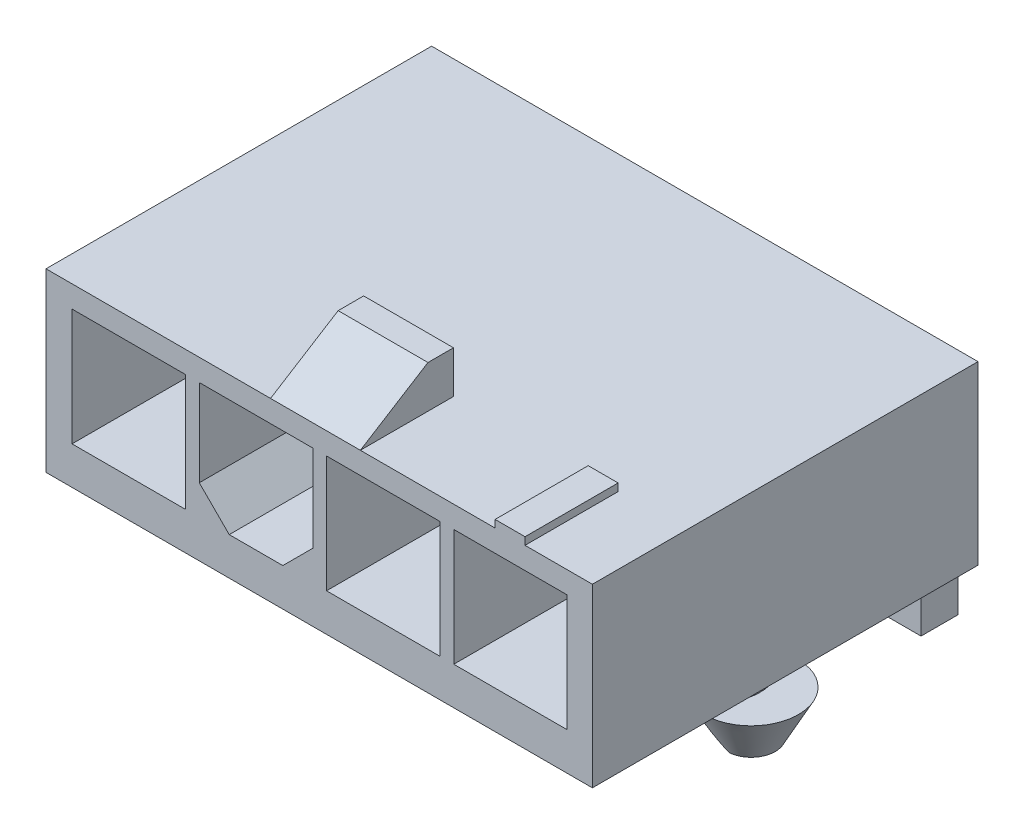
SolidWorks part; units mm, degrees
ref_plane "Front Plane" through (0, 0, 0) normal (0, 0, 1) x (1, 0, 0)
ref_plane "Top Plane" through (0, 0, 0) normal (0, 1, 0) x (1, 0, 0)
ref_plane "Right Plane" through (0, 0, 0) normal (1, 0, 0) x (0, 0, -1)
sketch "Sketch1" plane through (0, 0, 0) normal (0, 1, 0) x (1, 0, 0)
  line L1 (0, 0) -> (18.25, 0)
  line L2 (0, 0) -> (0, 12.88)
  line L3 (0, 12.88) -> (18.25, 12.88)
  line L4 (18.25, 0) -> (18.25, 12.88)
extrude "Boss-Extrude1" add sketch "Sketch1" along normal blind 5.89
sketch "Sketch2" plane through (0, 0, 0) normal (0, 0, 1) x (1, 0, 0)
  line L0 (4.66, 5.1605) -> (5.12, 5.1605) construction
  line L1 (0.87, 5.1605) -> (4.66, 5.1605)
  line L2 (0.87, 5.1605) -> (0.87, 1.2605)
  line L3 (0.87, 1.2605) -> (4.66, 1.2605)
  line L4 (4.66, 5.1605) -> (4.66, 1.2605)
  line L5 (5.12, 5.1605) -> (8.91, 5.1605)
  line L6 (5.12, 5.1605) -> (5.12, 1.2605) construction
  line L7 (5.12, 1.2605) -> (8.91, 1.2605) construction
  line L8 (8.91, 5.1605) -> (8.91, 1.2605) construction
  line L9 (9.37, 5.1605) -> (13.16, 5.1605)
  line L10 (9.37, 5.1605) -> (9.37, 1.2605)
  line L11 (9.37, 1.2605) -> (13.16, 1.2605)
  line L12 (13.16, 5.1605) -> (13.16, 1.2605)
  line L13 (13.62, 5.1605) -> (17.41, 5.1605)
  line L14 (13.62, 5.1605) -> (13.62, 1.2605)
  line L15 (13.62, 1.2605) -> (17.41, 1.2605)
  line L16 (17.41, 5.1605) -> (17.41, 1.2605)
  line L17 (8.91, 5.1605) -> (9.37, 5.1605) construction
  line L18 (13.16, 5.1605) -> (13.62, 5.1605) construction
  line L19 (4.66, 1.2605) -> (5.12, 1.2605) construction
  line L20 (8.91, 1.2605) -> (9.37, 1.2605) construction
  line L21 (5.12, 2.2605) -> (6.12, 1.2605)
  line L22 (13.16, 1.2605) -> (13.62, 1.2605) construction
  line L23 (5.12, 5.1605) -> (5.12, 2.2605)
  line L24 (6.12, 1.2605) -> (7.91, 1.2605)
  line L25 (7.91, 1.2605) -> (8.91, 2.2605)
  line L26 (8.91, 2.2605) -> (8.91, 5.1605)
extrude "Cut-Extrude1" cut sketch "Sketch2" against normal blind 9
sketch "Sketch3" plane through (0, 5.89, 0) normal (0, 1, 0) x (1, 0, 0)
  line L0 (0, 0) -> (18.25, 0) construction
  line L1 (7.5, 0) -> (10.5, 0)
  line L2 (7.5, 0) -> (7.5, 3.11)
  line L3 (7.5, 3.11) -> (10.5, 3.11)
  line L4 (10.5, 0) -> (10.5, 3.11)
extrude "Boss-Extrude2" add sketch "Sketch3" along normal blind 1.41
sketch "Sketch4" plane through (7.5, 0, 0) normal (-1, 0, 0) x (0, 0, 1)
  line L0 (-2.2584, 7.3) -> (0, 5.89)
  line L1 (-3.11, 7.3) -> (0, 7.3) construction
  line L2 (0, 7.3) -> (0, 5.89) construction
  line L3 (0, 5.89) -> (0, 7.3)
  line L4 (0, 7.3) -> (-2.2584, 7.3)
extrude "Cut-Extrude2" cut sketch "Sketch4" against normal blind 3
sketch "Sketch5" plane through (0, 0, -12.88) normal (0, 0, -1) x (-1, 0, 0)
  line L1 (-3.4, 3.26) -> (-2.17, 3.26)
  line L2 (-3.4, 3.26) -> (-3.4, 2.03)
  line L3 (-3.4, 2.03) -> (-2.17, 2.03)
  line L4 (-2.17, 3.26) -> (-2.17, 2.03)
  line L18 (-7.6052, 3.2578) -> (-6.3752, 3.2578)
  line L19 (-7.6052, 3.2578) -> (-7.6052, 2.0278)
  line L20 (-7.6052, 2.0278) -> (-6.3752, 2.0278)
  line L21 (-6.3752, 3.2578) -> (-6.3752, 2.0278)
  line L22 (-11.8105, 3.2556) -> (-10.5805, 3.2556)
  line L23 (-11.8105, 3.2556) -> (-11.8105, 2.0256)
  line L24 (-11.8105, 2.0256) -> (-10.5805, 2.0256)
  line L25 (-10.5805, 3.2556) -> (-10.5805, 2.0256)
  line L26 (-16.0157, 3.2535) -> (-14.7857, 3.2535)
  line L27 (-16.0157, 3.2535) -> (-16.0157, 2.0235)
  line L28 (-16.0157, 2.0235) -> (-14.7857, 2.0235)
  line L29 (-14.7857, 3.2535) -> (-14.7857, 2.0235)
  dimension "D1" = 4
sketch "Sketch7" plane through (0, 0, 0) normal (-1, 0, 0) x (0, 0, 1)
  line L0 (-4.3, 2.72) -> (-12.7005, 2.72)
  line L1 (-13.88, 1.5405) -> (-13.88, -3.3375)
  arc A0 (-12.7005, 2.72) -> (-13.88, 1.5405) centre (-12.7005, 1.5405) ccw
ref_plane "Plane1" through (0, -3.3375, 0) normal (0, -1, 0) x (1, 0, 0)
sketch "Sketch8" plane through (0, -3.3375, 0) normal (0, -1, 0) x (1, 0, 0)
  line L1 (14.7821, -13.2152) -> (16.0121, -13.2152)
  line L2 (14.7821, -13.2152) -> (14.7821, -14.4452)
  line L3 (14.7821, -14.4452) -> (16.0121, -14.4452)
  line L4 (16.0121, -13.2152) -> (16.0121, -14.4452)
  line L18 (10.5768, -13.2174) -> (11.8068, -13.2174)
  line L19 (10.5768, -13.2174) -> (10.5768, -14.4474)
  line L20 (10.5768, -14.4474) -> (11.8068, -14.4474)
  line L21 (11.8068, -13.2174) -> (11.8068, -14.4474)
  line L22 (6.3716, -13.2196) -> (7.6016, -13.2196)
  line L23 (6.3716, -13.2196) -> (6.3716, -14.4496)
  line L24 (6.3716, -14.4496) -> (7.6016, -14.4496)
  line L25 (7.6016, -13.2196) -> (7.6016, -14.4496)
  line L26 (2.1663, -13.2217) -> (3.3963, -13.2217)
  line L27 (2.1663, -13.2217) -> (2.1663, -14.4517)
  line L28 (2.1663, -14.4517) -> (3.3963, -14.4517)
  line L29 (3.3963, -13.2217) -> (3.3963, -14.4517)
  dimension "D1" = 4
extrude "Cut-Extrude3" cut sketch "Sketch5" against normal blind 4
sweep "Sweep2" add profiles "Sketch8" path "Sketch7"
sketch "Sketch9" plane through (0, 5.89, 0) normal (0, 1, 0) x (1, 0, 0)
  line L0 (10.5, 0) -> (18.25, 0) construction
  line L1 (15, 0) -> (16, 0)
  line L2 (15, 0) -> (15, 3.11)
  line L3 (15, 3.11) -> (16, 3.11)
  line L4 (16, 0) -> (16, 3.11)
  line L5 (10.5, 3.11) -> (7.5, 3.11) construction
extrude "Boss-Extrude3" add sketch "Sketch9" along normal blind 0.25
sketch "Sketch10" plane through (0, 0, 0) normal (0, -1, 0) x (1, 0, 0)
  line L0 (0, -7.15) -> (18.25, -7.15) construction
  line L1 (0, -12.88) -> (0, 0) construction
  line L2 (18.25, 0) -> (18.25, -12.88) construction
  line L3 (2.55, 0) -> (2.55, -12.88) construction
  line L4 (0, 0) -> (18.25, 0) construction
  line L5 (18.25, -12.88) -> (0, -12.88) construction
  line L6 (2.55, -5.7358) -> (2.55, -8.5642)
  line L7 (3.55, 0) -> (3.55, -12.88) construction
  line L8 (3.05, 0) -> (3.05, -12.88) construction
  line L9 (15.2, 0) -> (15.2, -12.88) construction
  line L10 (15.7, 0) -> (15.7, -12.88) construction
  line L11 (14.7, 0) -> (14.7, -12.88) construction
  line L12 (15.2, -3.5626) -> (18.25, -3.5626) construction
  line L13 (3.05, -3.5626) -> (0, -3.5626) construction
  line L14 (2.55, -1.1734) -> (3.05, -1.1734) construction
  line L15 (14.7, -1.1734) -> (15.2, -1.1734) construction
  line L16 (3.05, -2.7484) -> (3.55, -2.7484) construction
  line L17 (15.2, -2.7484) -> (15.7, -2.7484) construction
  line L18 (3.55, -5.7358) -> (3.55, -8.5642)
  line L19 (14.7, -5.7358) -> (14.7, -8.5642)
  line L20 (15.7, -5.7358) -> (15.7, -8.5642)
  circle A0 centre (3.05, -7.15) radius 1.5 construction
  circle A1 centre (15.2, -7.15) radius 1.5 construction
  arc A2 (2.55, -5.7358) -> (2.55, -8.5642) centre (3.05, -7.15) ccw
  arc A3 (3.55, -8.5642) -> (3.55, -5.7358) centre (3.05, -7.15) ccw
  arc A4 (14.7, -5.7358) -> (14.7, -8.5642) centre (15.2, -7.15) ccw
  arc A5 (15.7, -8.5642) -> (15.7, -5.7358) centre (15.2, -7.15) ccw
extrude "Boss-Extrude5" add sketch "Sketch10" along normal blind 1.5875
sketch "Sketch12" plane through (0, -1.5875, 0) normal (0, -1, 0) x (1, 0, 0)
  line L0 (2.55, -5.7358) -> (2.55, -8.5642)
  line L1 (3.55, -5.7358) -> (3.55, -8.5642) construction
  line L2 (3.55, -5.7358) -> (3.55, -8.5642)
  line L3 (14.7, -8.5642) -> (14.7, -5.7358) construction
  line L4 (14.7, -5.7358) -> (14.7, -8.5642)
  line L5 (15.7, -5.7358) -> (15.7, -8.5642)
  arc A0 (2.55, -8.5642) -> (2.55, -5.7358) centre (1.846, -7.15) cw
  arc A1 (3.55, -5.7358) -> (3.55, -8.5642) centre (4.254, -7.15) cw
  arc A2 (3.55, -8.5642) -> (3.55, -5.7358) centre (3.05, -7.15) ccw construction
  arc A3 (15.7, -5.7358) -> (15.7, -8.5642) centre (16.404, -7.15) cw
  arc A4 (14.7, -8.5642) -> (14.7, -5.7358) centre (13.996, -7.15) cw
  arc A5 (14.7, -5.7358) -> (14.7, -8.5642) centre (15.2, -7.15) ccw construction
extrude "Boss-Extrude6" add sketch "Sketch12" along normal blind 1.46 draft 28
